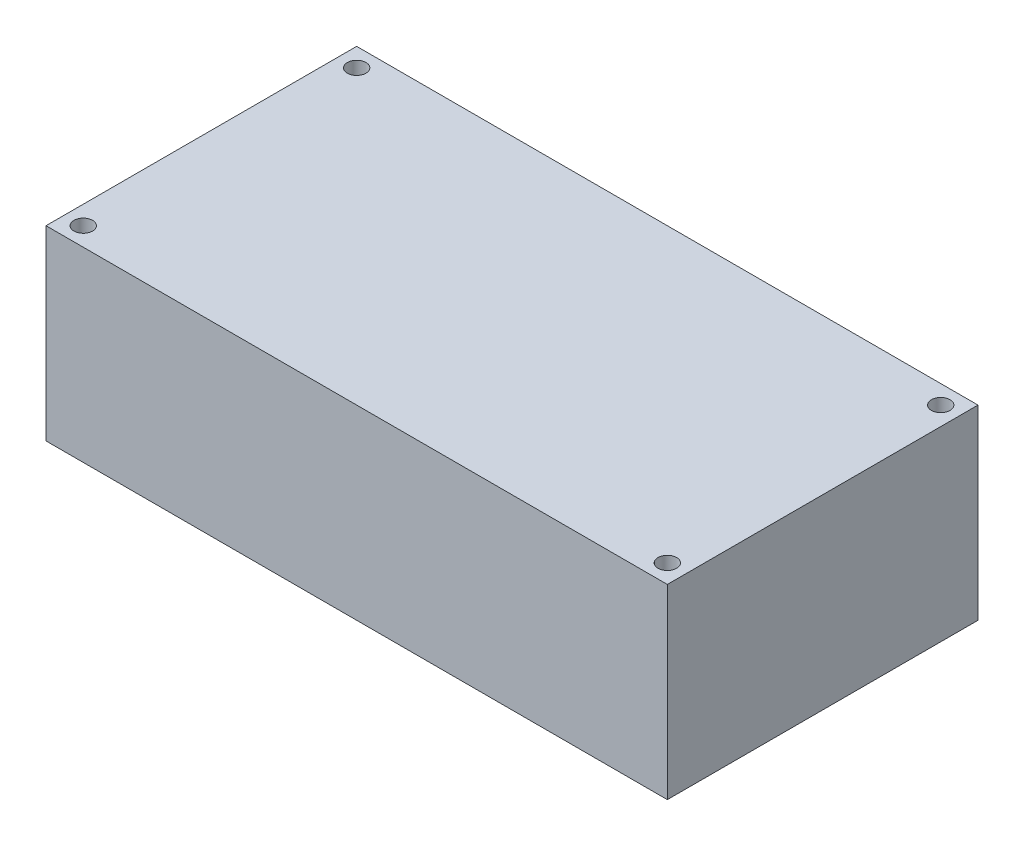
SolidWorks part; units mm, degrees
ref_plane "Plan de face" through (0, 0, 0) normal (0, 0, 1) x (1, 0, 0)
ref_plane "Plan de dessus" through (0, 0, 0) normal (0, 1, 0) x (1, 0, 0)
ref_plane "Plan de droite" through (0, 0, 0) normal (1, 0, 0) x (0, 0, -1)
sketch "Esquisse2" plane through (0, 0, 0) normal (0, 1, 0) x (1, 0, 0)
  line L1 (-50, 25) -> (50, 25)
  line L2 (-50, 25) -> (-50, -25)
  line L3 (-50, -25) -> (50, -25)
  line L4 (50, 25) -> (50, -25)
  dimension "D1" = 100
  dimension "D2" = 50
  dimension "D3" = 50
  dimension "D4" = 25
extrude "Boss.-Extru.1" add sketch "Esquisse2" along normal blind 30
sketch "Esquisse3" plane through (0, 30, 0) normal (0, 1, 0) x (1, 0, 0)
  line L0 (-50, 25) -> (-50, -25) construction
  line L1 (-47, 22) -> (47, 22) construction
  line L2 (-47, 22) -> (-47, -22) construction
  line L3 (-47, -22) -> (47, -22) construction
  line L4 (47, 22) -> (47, -22) construction
  line L5 (50, 25) -> (-50, 25) construction
  line L7 (-50, -25) -> (50, -25) construction
  line L8 (0, 38.0881) -> (0, -39.8087) construction
  circle A0 centre (-47, 22) radius 1.5
  circle A1 centre (-47, -22) radius 1.5
  circle A2 centre (47, -22) radius 1.5
  circle A3 centre (47, 22) radius 1.5
  dimension "D5" = 3
  dimension "D6" = 3
  dimension "D3" = 44
  dimension "D7" = 94
  dimension "D1" = 3
  dimension "D2" = 3
  dimension "D4" = 3
extrude "Enlèv. mat.-Extru.1" cut sketch "Esquisse3" against normal blind 30
equation "\"D3@Esquisse2\"=\"D1@Esquisse2\"/2"
equation "\"D4@Esquisse2\"=\"D2@Esquisse2\"/2"
